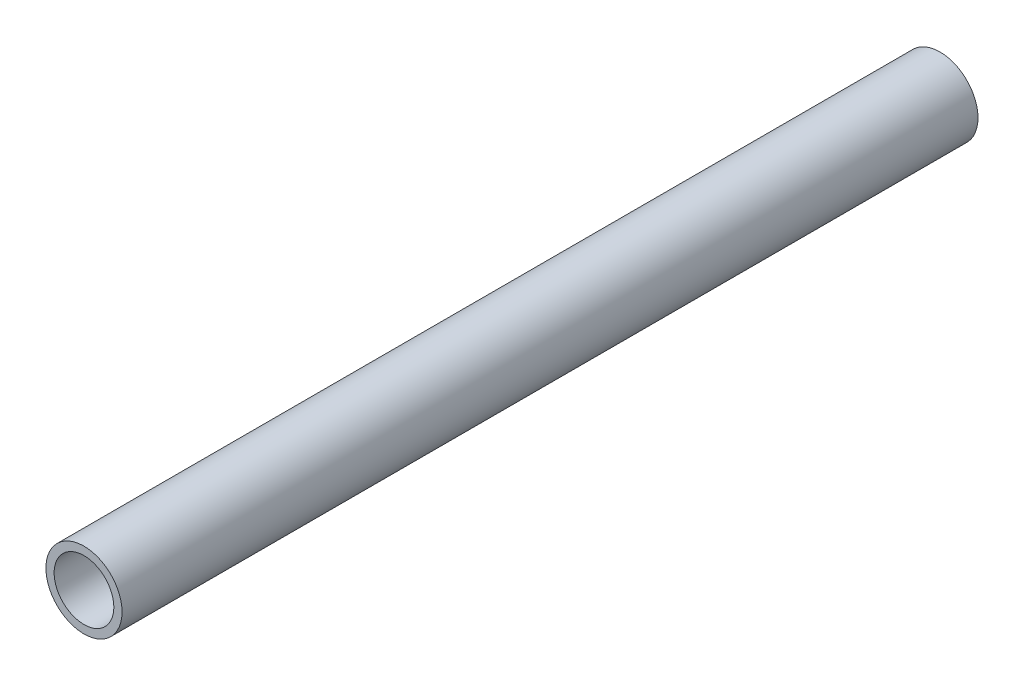
SolidWorks part; units mm, degrees
ref_plane "Front Plane" through (0, 0, 0) normal (0, 0, 1) x (1, 0, 0)
ref_plane "Top Plane" through (0, 0, 0) normal (0, 1, 0) x (1, 0, 0)
ref_plane "Right Plane" through (0, 0, 0) normal (1, 0, 0) x (0, 0, -1)
sketch "Sketch1" plane through (0, 0, 0) normal (0, 0, 1) x (1, 0, 0)
  circle A0 centre (0, 0) radius 13.335
  dimension "Pipe OD" = 26.67
extrude "Extrude-Thin1" add sketch "Sketch1" along normal mid plane 300 thin thin type one direction reverse wall 2.8702
